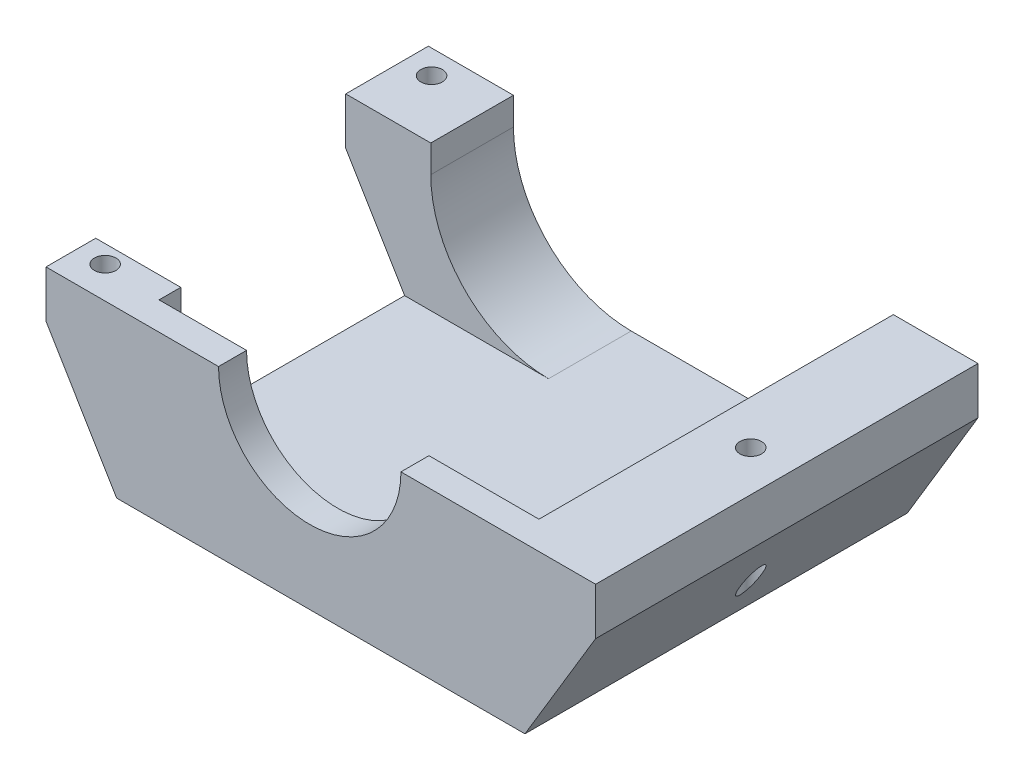
SolidWorks part; units mm, degrees
ref_plane "Front Plane" through (0, 0, 0) normal (0, 0, 1) x (1, 0, 0)
ref_plane "Top Plane" through (0, 0, 0) normal (0, 1, 0) x (1, 0, 0)
ref_plane "Right Plane" through (0, 0, 0) normal (1, 0, 0) x (0, 0, -1)
sketch "Sketch1" plane through (0, 0, 0) normal (0, 1, 0) x (1, 0, 0)
  line L1 (0, 0) -> (139.9914, 0)
  line L2 (0, 0) -> (0, 97.3933)
  line L3 (0, 97.3933) -> (139.9914, 97.3933)
  line L4 (139.9914, 0) -> (139.9914, 97.3933)
extrude "PiCover" add sketch "Sketch1" along normal blind 40 and the other way blind 2
sketch "Sketch2" plane through (0, 40, 0) normal (0, 1, 0) x (1, 0, 0)
  line L0 (139.9914, 97.3933) -> (0, 97.3933) construction
  line L1 (21.6644, 97.3933) -> (118.4243, 97.3933)
  line L2 (21.6644, 97.3933) -> (21.6644, 7.1339)
  line L3 (21.6644, 7.1339) -> (118.4243, 7.1339)
  line L4 (118.4243, 97.3933) -> (118.4243, 7.1339)
extrude "OpeningForPi" cut sketch "Sketch2" against normal blind 37
sketch "Sketch3" plane through (0, 0, 0) normal (0, 0, 1) x (1, 0, 0)
  line L0 (0, 40) -> (139.9914, 40) construction
  circle A0 centre (67.1752, 40) radius 23.2306
extrude "HoleToAccessSDCard" cut sketch "Sketch3" against normal up to surface (7.1339 mm away) up to face at (70.0444, 21.5, -7.1339)
sketch "Sketch4" plane through (0, -2, 0) normal (0, -1, 0) x (1, 0, 0)
  line L0 (139.9914, -97.3933) -> (0, -97.3933) construction
  line L1 (139.9914, 0) -> (121.9914, 0)
  line L2 (139.9914, 0) -> (139.9914, -97.3933)
  line L3 (139.9914, -97.3933) -> (121.9914, -97.3933)
  line L4 (121.9914, 0) -> (121.9914, -97.3933)
  line L5 (0, 0) -> (139.9914, 0) construction
  line L6 (0, -97.3933) -> (18, -97.3933)
  line L7 (0, -97.3933) -> (0, 0)
  line L8 (0, 0) -> (18, 0)
  line L9 (18, -97.3933) -> (18, 0)
extrude "CutAwaysThatDefineScrewPlates" cut sketch "Sketch4" against normal blind 30
sketch "Sketch11" plane through (0, 0, 0) normal (0, 0, 1) x (1, 0, 0)
  line L0 (0, 28) -> (18, 28)
  line L1 (18, 28) -> (18, -2)
  line L2 (18, -2) -> (0, 28)
  line L3 (139.9914, 28) -> (121.9914, 28)
  line L4 (121.9914, 28) -> (121.9914, -2)
  line L5 (121.9914, -2) -> (139.9914, 28)
extrude "Boss-Extrude1" add sketch "Sketch11" against normal up to surface (97.3933 mm away) up to face at (70.0119, 22.8333, -97.3933)
sketch "Sketch6" plane through (21.6644, 0, 0) normal (1, 0, 0) x (0, 0, -1)
  line L0 (97.3933, 3) -> (7.1339, 3) construction
  line L1 (76.3395, 3) -> (12.6666, 3)
  line L2 (76.3395, 3) -> (76.3395, 40)
  line L3 (76.3395, 40) -> (12.6666, 40)
  line L4 (12.6666, 3) -> (12.6666, 40)
  line L5 (97.3933, 40) -> (7.1339, 40) construction
extrude "HoleForPowerHDMIAudio" cut sketch "Sketch6" against normal blind 30
sketch "Sketch5" plane through (0, 40, 0) normal (0, 1, 0) x (1, 0, 0)
  circle A0 centre (129.6245, 49.8786) radius 2.75
extrude "Cut-Extrude5" cut sketch "Sketch5" against normal through all
sketch "Sketch7" plane through (0, 40, 0) normal (0, 1, 0) x (1, 0, 0)
  circle A0 centre (6.9345, 8.1289) radius 2.75
  circle A1 centre (6.9345, 91.2756) radius 2.75
extrude "Cut-Extrude7" cut sketch "Sketch7" against normal blind 30
fillet "Fillet1" radius 30 1 edges at (21.6644, 3, -86.8664)
fillet "Fillet2" radius 30 1 edges at (118.4243, 3, -52.2636)
